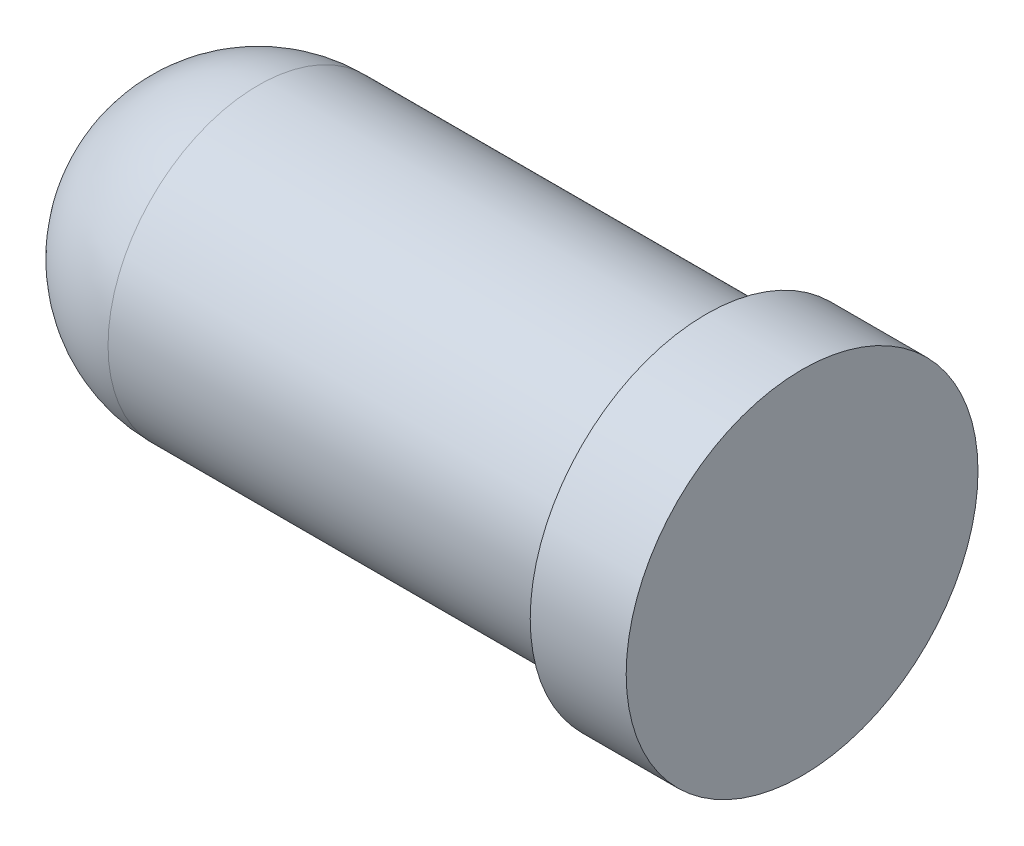
SolidWorks part; units mm, degrees
ref_plane "Front" through (0, 0, 0) normal (0, 0, 1) x (1, 0, 0)
ref_plane "Top" through (0, 0, 0) normal (0, 1, 0) x (1, 0, 0)
ref_plane "Right" through (0, 0, 0) normal (1, 0, 0) x (0, 0, -1)
sketch "Sketch1" plane through (0, 0, 0) normal (1, 0, 0) x (0, 0, -1)
  circle A0 centre (0, 0) radius 2.35
extrude "Boss-Extrude1" add sketch "Sketch1" along normal blind 7
sketch "Sketch2" plane through (7, 0, 0) normal (1, 0, 0) x (0, 0, -1)
  circle A0 centre (0, 0) radius 2.75
  dimension "D1" = 5.5
extrude "Boss-Extrude2" add sketch "Sketch2" along normal blind 1.5
sketch "Sketch15" plane through (0, 0, 0) normal (0, 0, 1) x (1, 0, 0)
  line L0 (0, 2.35) -> (0, -2.35) construction
  line L1 (0, 2.35) -> (0, -2.35)
  arc A0 (0, 2.35) -> (0, -2.35) centre (0, 0) ccw
revolve "Revolve1" add sketch "Sketch15" angle 360 about L1
